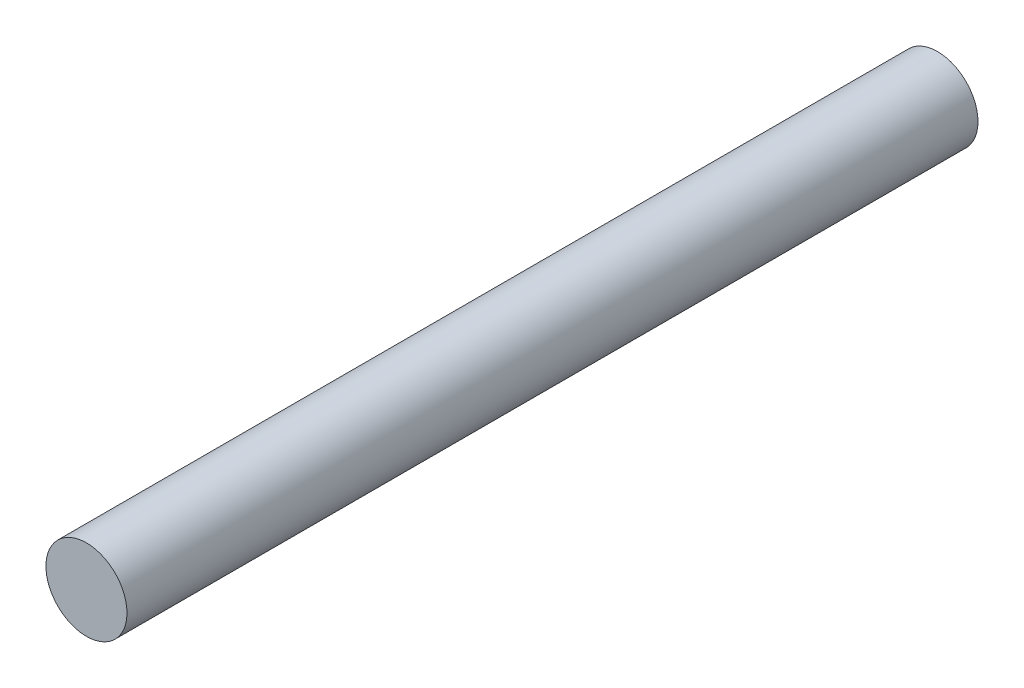
SolidWorks part; units mm, degrees
material "AISI 316 退火不锈钢条 (SS)"
ref_plane "前视基准面" through (0, 0, 0) normal (0, 0, 1) x (1, 0, 0)
ref_plane "上视基准面" through (0, 0, 0) normal (0, 1, 0) x (1, 0, 0)
ref_plane "右视基准面" through (0, 0, 0) normal (1, 0, 0) x (0, 0, -1)
sketch "草图1" plane through (0, 0, 0) normal (0, 0, 1) x (1, 0, 0)
  circle A0 centre (0, 0) radius 20
  dimension "D1" = 40
extrude "凸台-拉伸2" add sketch "草图1" along normal blind 420
